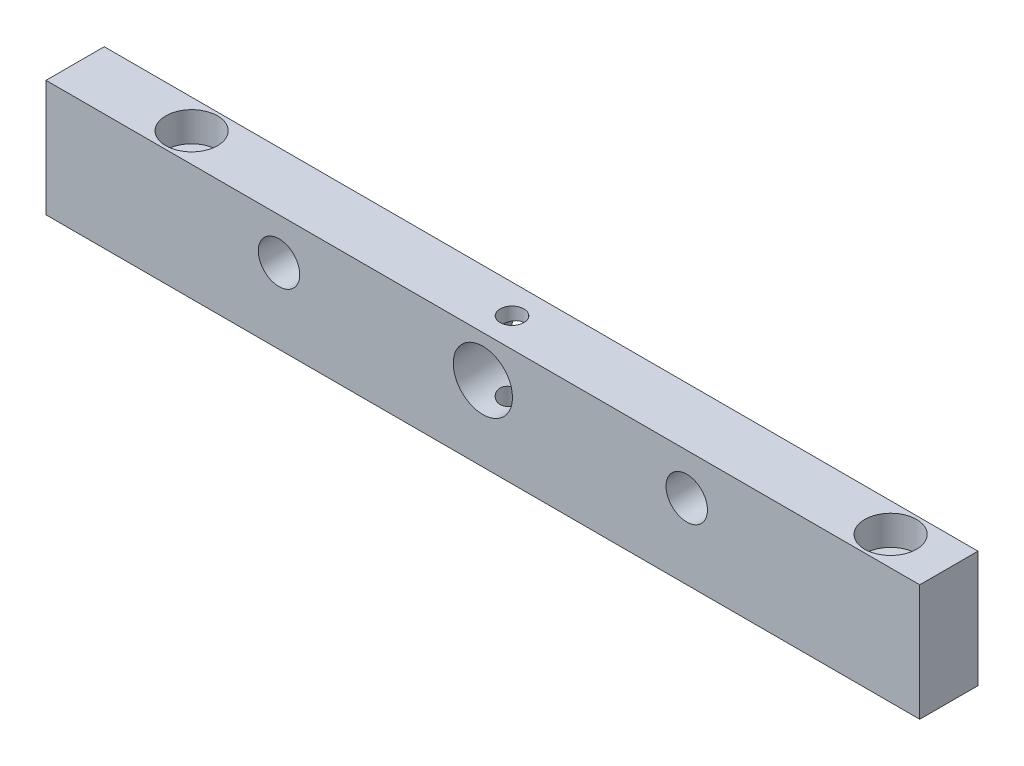
SolidWorks part; units mm, degrees
ref_plane "Front Plane" through (0, 0, 0) normal (0, 0, 1) x (1, 0, 0)
ref_plane "Top Plane" through (0, 0, 0) normal (0, 1, 0) x (1, 0, 0)
ref_plane "Right Plane" through (0, 0, 0) normal (1, 0, 0) x (0, 0, -1)
sketch "Sketch1" plane through (0, 0, 0) normal (0, 1, 0) x (1, 0, 0)
  line L1 (-15.0786, 5.4889) -> (172.4214, 5.4889)
  line L2 (-15.0786, 5.4889) -> (-15.0786, -7.0111)
  line L3 (-15.0786, -7.0111) -> (172.4214, -7.0111)
  line L4 (172.4214, 5.4889) -> (172.4214, -7.0111)
  dimension "D1" = 12.5
  dimension "D2" = 187.5
extrude "Boss-Extrude1" add sketch "Sketch1" along normal blind 25
sketch "Sketch2" plane through (0, 25, 0) normal (0, 1, 0) x (1, 0, 0)
  line L0 (-15.0786, -0.7611) -> (172.4214, -0.7611) construction
  line L1 (-15.0786, 5.4889) -> (-15.0786, -7.0111) construction
  line L2 (172.4214, -7.0111) -> (172.4214, 5.4889) construction
  point P6 (9.9214, -0.7611)
  point P7 (159.9214, -0.7611)
  point P8 (78.6714, -0.7611)
  dimension "D1" = 25
  dimension "D2" = 12.5
hole_wizard "CBORE for 1/4 Socket Head Cap Screw1" positions "3DSketch2" profile "Sketch3" counterbore size "1/4" standard "ANSI Inch" end condition up to next
sketch3d "3DSketch2"
  point P0 (9.9214, 25, 0.7611)
  point P3 (159.9214, 25, 0.7611)
sketch "Sketch3" plane through (9.9214, 25, 0.7611) normal (1, 0, 0) x (0, 0, 1)
  line L0 (0, 0) -> (0, 25)
  line L1 (0, 25) -> (3.3782, 25)
  line L3 (3.3782, 25) -> (3.3782, 6.35)
  line L4 (3.3782, 6.35) -> (5.5562, 6.35)
  line L5 (5.5562, 6.35) -> (5.5562, 0)
  line L7 (5.5562, 0) -> (0, 0)
  line L11 (0, -6.35) -> (0, 107.95) construction
  dimension "Thru Hole Dia." = 6.7564
  dimension "Thru Hole Depth" = 25
  dimension "C'Bore Dia." = 11.1125
  dimension "C'Bore Depth" = 6.35
sketch "Sketch4" plane through (0, 0, -5.4889) normal (0, 0, -1) x (-1, 0, 0)
  line L0 (-172.4214, 16.11) -> (15.0786, 16.11)
  line L1 (-172.4214, 25) -> (-172.4214, 0) construction
  line L2 (15.0786, 25) -> (15.0786, 0) construction
  line L3 (-172.4214, 25) -> (15.0786, 25) construction
  line L4 (-122.4214, 25) -> (-122.4214, 0) construction
  line L5 (-172.4214, 0) -> (15.0786, 0) construction
  line L6 (-34.9214, 25) -> (-34.9214, 0) construction
  line L7 (-78.6714, 25) -> (-78.6714, 0) construction
  circle A0 centre (-122.4214, 16.11) radius 4.445
  circle A1 centre (-34.9214, 16.11) radius 4.445
  circle A2 centre (-78.6714, 16.11) radius 6.35
  dimension "D4" = 8.89
  dimension "D5" = 8.89
  dimension "D6" = 12.7
  dimension "D1" = 8.89
  dimension "D2" = 50
  dimension "D3" = 50
extrude "Cut-Extrude1" cut sketch "Sketch4" against normal up to next contours L0 A1 | L0 A1 | A0 | A2
hole_wizard "1/4-20 Tapped Hole1" positions "3DSketch3" profile "Sketch8" tap size "1/4-20" standard "ANSI Inch" end condition through all
sketch3d "3DSketch3"
  point P0 (78.6714, 25, 0.7611)
sketch "Sketch8" plane through (78.6714, 25, 0.7611) normal (1, 0, 0) x (0, 0, 1)
  line L0 (0, 0) -> (0, 25)
  line L1 (0, 25) -> (2.5527, 25)
  line L2 (2.5527, 25) -> (2.5527, 0)
  line L5 (2.5527, 0) -> (0, 0)
  line L11 (0, -6.35) -> (0, 107.95) construction
  dimension "Thru Tap Drill Dia." = 5.1054
  dimension "Thru Tap Drill Depth" = 25
cosmetic thread "Hole Thread1" parameters "D2"=6.35
